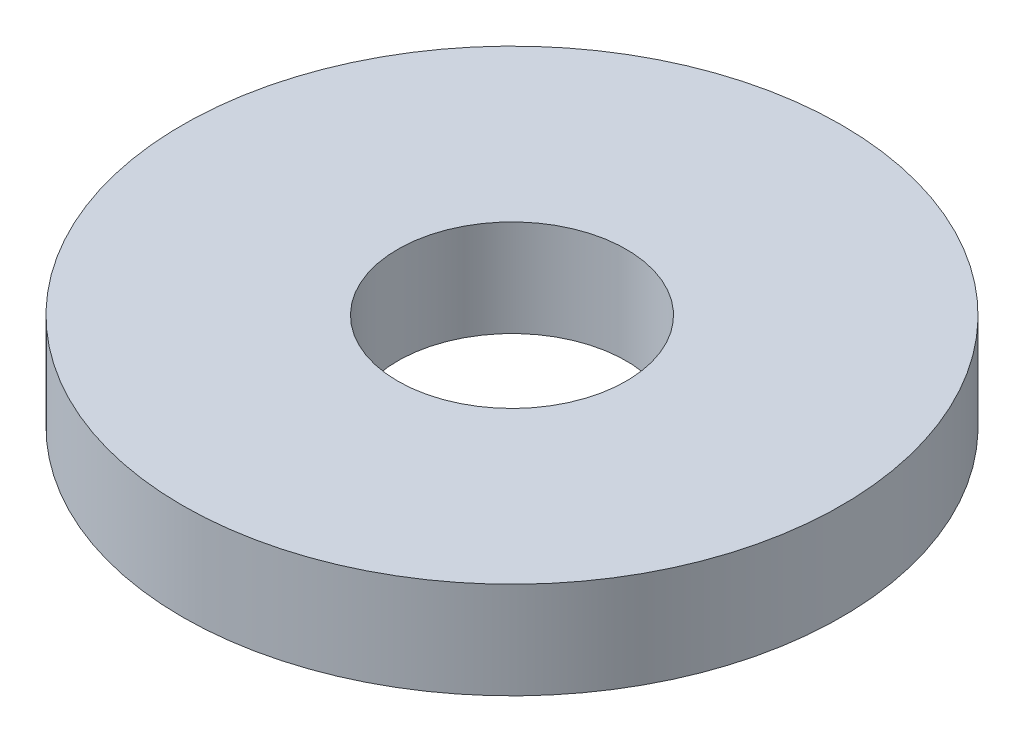
SolidWorks part; units mm, degrees
material "POLYURETHANE (11671)"
ref_plane "Front" through (0, 0, 0) normal (0, 0, 1) x (1, 0, 0)
ref_plane "Top" through (0, 0, 0) normal (0, 1, 0) x (1, 0, 0)
ref_plane "Right" through (0, 0, 0) normal (1, 0, 0) x (0, 0, -1)
sketch "Sketch1" plane through (0, 0, 0) normal (0, 1, 0) x (1, 0, 0)
  circle A0 centre (0, 0) radius 3.75
  dimension "D1" = 7.5
extrude "Boss-Extrude1" add sketch "Sketch1" along normal blind 1.1
sketch "Sketch2" plane through (0, 1.1, 0) normal (0, 1, 0) x (1, 0, 0)
  circle A0 centre (0, 0) radius 1.3
  dimension "D1" = 2.6
extrude "Cut-Extrude1" cut sketch "Sketch2" against normal through all
